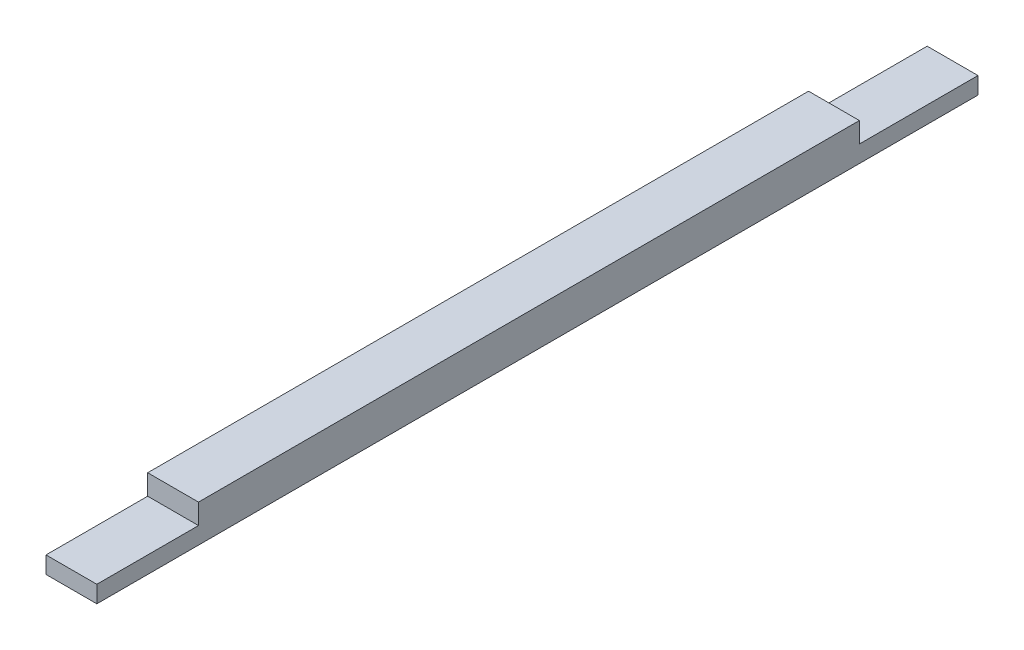
SolidWorks part; units mm, degrees
ref_plane "Plan de face" through (0, 0, 0) normal (0, 0, 1) x (1, 0, 0)
ref_plane "Plan de dessus" through (0, 0, 0) normal (0, 1, 0) x (1, 0, 0)
ref_plane "Plan de droite" through (0, 0, 0) normal (1, 0, 0) x (0, 0, -1)
sketch "Esquisse1" plane through (0, 0, 0) normal (0, 0, 1) x (1, 0, 0)
  line L1 (0, 0) -> (3, 0)
  line L2 (0, 0) -> (0, -1)
  line L3 (0, -1) -> (3, -1)
  line L4 (3, 0) -> (3, -1)
  dimension "D1" = 1
  dimension "D2" = 3
extrude "Boss.-Extru.1" add sketch "Esquisse1" along normal blind 52
sketch "Esquisse2" plane through (0, 0, 0) normal (0, 1, 0) x (1, 0, 0)
  line L0 (0, -52) -> (0, 0) construction
  line L1 (0, -7) -> (3, -7)
  line L2 (0, -7) -> (0, -46)
  line L3 (0, -46) -> (3, -46)
  line L4 (3, -7) -> (3, -46)
  line L5 (3, -52) -> (3, 0) construction
  line L6 (3, -52) -> (0, -52) construction
  line L7 (3, 0) -> (0, 0) construction
  dimension "D1" = 6
  dimension "D2" = 7
extrude "Boss.-Extru.2" add sketch "Esquisse2" along normal blind 1.2
